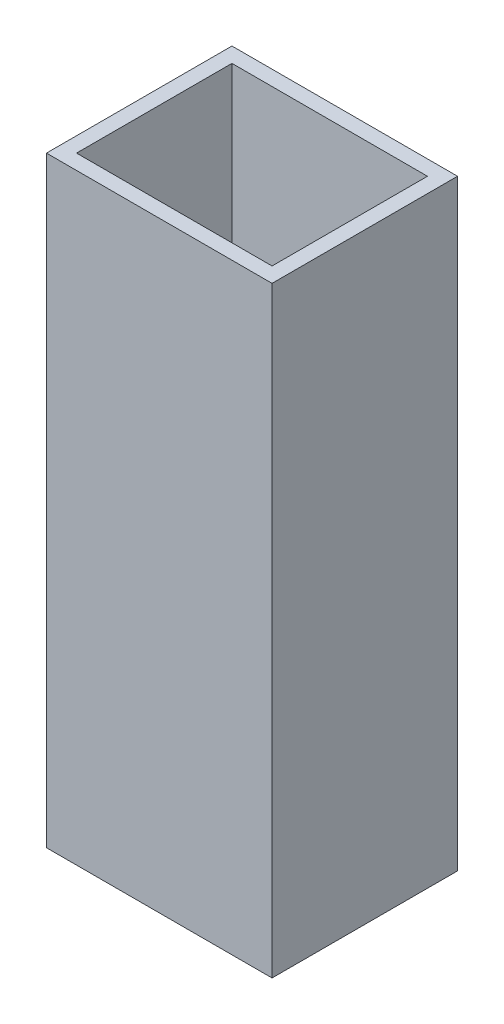
SolidWorks part; units mm, degrees
ref_plane "Front Plane" through (0, 0, 0) normal (0, 0, 1) x (1, 0, 0)
ref_plane "Top Plane" through (0, 0, 0) normal (0, 1, 0) x (1, 0, 0)
ref_plane "Right Plane" through (0, 0, 0) normal (1, 0, 0) x (0, 0, -1)
sketch "Sketch2" plane through (0, 0, 0) normal (0, 1, 0) x (1, 0, 0)
  line L1 (0, 0) -> (45, 0)
  line L2 (0, 0) -> (0, 37)
  line L3 (0, 37) -> (45, 37)
  line L4 (45, 0) -> (45, 37)
  dimension "D1" = 45
  dimension "D2" = 37
extrude "Boss-Extrude1" add sketch "Sketch2" along normal blind 3
sketch "Sketch3" plane through (0, 3, 0) normal (0, 1, 0) x (1, 0, 0)
  line L1 (0, 37) -> (45, 37)
  line L2 (0, 37) -> (0, 0)
  line L3 (0, 0) -> (45, 0)
  line L4 (45, 37) -> (45, 0)
  line L5 (3, 34) -> (42, 34)
  line L6 (3, 34) -> (3, 3)
  line L7 (3, 3) -> (42, 3)
  line L8 (42, 34) -> (42, 3)
  dimension "D1" = 39
  dimension "D2" = 31
  dimension "D3" = 3
  dimension "D4" = 3
extrude "Boss-Extrude2" add sketch "Sketch3" along normal blind 117
